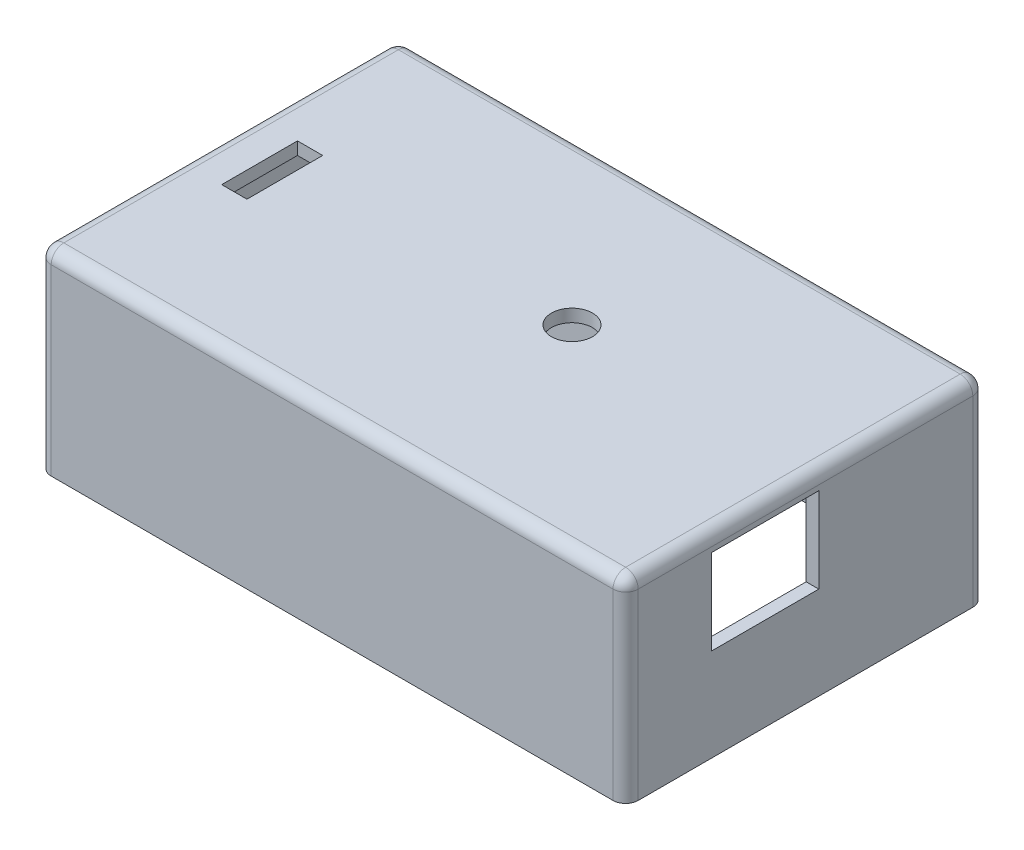
SolidWorks part; units mm, degrees
ref_plane "Front Plane" through (0, 0, 0) normal (0, 0, 1) x (1, 0, 0)
ref_plane "Top Plane" through (0, 0, 0) normal (0, 1, 0) x (1, 0, 0)
ref_plane "Right Plane" through (0, 0, 0) normal (1, 0, 0) x (0, 0, -1)
sketch "Sketch1" plane through (0, 0, 0) normal (0, 1, 0) x (1, 0, 0)
  line L1 (-46.5, -28.5) -> (46.5, -28.5)
  line L2 (-46.5, -28.5) -> (-46.5, 28.5)
  line L3 (-46.5, 28.5) -> (46.5, 28.5)
  line L4 (46.5, -28.5) -> (46.5, 28.5)
  line L5 (-46.5, -28.5) -> (46.5, 28.5) construction
  line L6 (-46.5, 28.5) -> (46.5, -28.5) construction
  point P0 (0, 0)
  dimension "D1" = 93
  dimension "D2" = 57
extrude "Boss-Extrude1" add sketch "Sketch1" along normal blind 31
shell "Shell1" thickness 2
sketch "Sketch2" plane through (46.5, 0, 0) normal (1, 0, 0) x (0, 0, -1)
  line L0 (-28.5, 0) -> (28.5, 0) construction
  line L1 (-14.9, 14.7) -> (2.1, 14.7)
  line L2 (-14.9, 14.7) -> (-14.9, 28.2)
  line L3 (-14.9, 28.2) -> (2.1, 28.2)
  line L4 (2.1, 14.7) -> (2.1, 28.2)
  line L5 (-14.9, 14.7) -> (2.1, 28.2) construction
  line L6 (-14.9, 28.2) -> (2.1, 14.7) construction
  line L7 (-28.5, 31) -> (-28.5, 0) construction
  point P0 (-6.4, 21.45)
  dimension "D1" = 17
  dimension "D2" = 13.5
  dimension "D3" = 14.7
  dimension "D4" = 13.6
extrude "Cut-Extrude1" cut sketch "Sketch2" against normal up to surface (2 mm away) up to face at (44.5, 14.5, 0)
sketch "Sketch3" plane through (0, 31, 0) normal (0, 1, 0) x (1, 0, 0)
  line L0 (-46.5, -28.5) -> (46.5, -28.5) construction
  line L2 (-46.5, 28.5) -> (-46.5, -28.5) construction
  circle A0 centre (7, 2.5) radius 3.25
  dimension "D1" = 6.5
  dimension "D2" = 31
  dimension "D3" = 53.5
extrude "Cut-Extrude2" cut sketch "Sketch3" against normal up to surface (2 mm away) up to face at (0, 29, 0)
sketch "Sketch4" plane through (0, 31, 0) normal (0, 1, 0) x (1, 0, 0)
  line L0 (-46.5, 28.5) -> (-46.5, -28.5) construction
  line L1 (-39.9873, -6) -> (-35.9873, -6)
  line L2 (-39.9873, -6) -> (-39.9873, 6)
  line L3 (-39.9873, 6) -> (-35.9873, 6)
  line L4 (-35.9873, -6) -> (-35.9873, 6)
  line L5 (-39.9873, -6) -> (-35.9873, 6) construction
  line L6 (-39.9873, 6) -> (-35.9873, -6) construction
  point P0 (-37.9873, 0)
  dimension "D1" = 4
  dimension "D2" = 12
  dimension "D3" = 6.5127
extrude "Cut-Extrude3" cut sketch "Sketch4" against normal up to surface (2 mm away) up to face at (7, 29, -5.75)
sketch "Sketch5" plane through (0, 0, -28.5) normal (0, 0, -1) x (-1, 0, 0)
  line L0 (46.5, 15.5) -> (-13.5295, 15.5) construction
  line L1 (46.5, 31) -> (46.5, 0) construction
  circle A0 centre (31.5, 15.5) radius 3
  circle A1 centre (16.5, 15.5) radius 3.25
  dimension "D1" = 6
  dimension "D2" = 6.5
  dimension "D3" = 15
  dimension "D4" = 15
extrude "Cut-Extrude4" cut sketch "Sketch5" against normal up to surface (2 mm away) up to face at (0, 14.5, -26.5)
sketch "Sketch6" plane through (-46.5, 0, 0) normal (-1, 0, 0) x (0, 0, 1)
  line L0 (-28.5, 15.5) -> (16.5493, 15.5) construction
  line L1 (-28.5, 31) -> (-28.5, 0) construction
  circle A0 centre (-18.5, 15.5) radius 5
  dimension "D1" = 10
  dimension "D2" = 10
extrude "Cut-Extrude5" cut sketch "Sketch6" against normal up to surface (2 mm away) up to face at (-44.5, 14.5, 0)
fillet "Fillet1" radius 2 8 edges at (46.5, 15.5, -28.5) (46.5, 15.5, 28.5) (-46.5, 15.5, -28.5) (-46.5, 15.5, 28.5) (46.5, 31, 0) (0, 31, 28.5) (0, 31, -28.5) (-46.5, 31, 0)
sketch "Sketch7" plane through (0, 0, 0) normal (0, -1, 0) x (1, 0, 0)
  line L0 (-45.6, 27.6) -> (-45.6, -27.6)
  line L1 (-44.5, 26.5) -> (44.5, 26.5)
  line L2 (-44.5, 26.5) -> (-44.5, -26.5)
  line L3 (-44.5, -26.5) -> (44.5, -26.5)
  line L4 (44.5, 26.5) -> (44.5, -26.5)
  line L5 (-45.6, -27.6) -> (45.6, -27.6)
  line L6 (45.6, 27.6) -> (45.6, -27.6)
  line L7 (-45.6, 27.6) -> (45.6, 27.6)
  dimension "D1" = 1.1
extrude "Cut-Extrude6" cut sketch "Sketch7" against normal blind 1.1
ref_plane "Plane1" through (0, 1.7, 0) normal (0, -1, 0) x (-1, 0, 0)
sketch "Sketch8" plane through (0, 1.7, 0) normal (0, -1, 0) x (-1, 0, 0)
  line L1 (-44.5, 26.5) -> (-34.5, 26.5)
  line L2 (-44.5, 26.5) -> (-44.5, 16.5)
  line L3 (-44.5, 16.5) -> (-34.5, 16.5)
  line L4 (-34.5, 26.5) -> (-34.5, 16.5)
  line L5 (-44.5, -26.5) -> (-34.5, -26.5)
  line L6 (-44.5, -26.5) -> (-44.5, -16.5)
  line L7 (-44.5, -16.5) -> (-34.5, -16.5)
  line L8 (-34.5, -26.5) -> (-34.5, -16.5)
  line L9 (44.5, -26.5) -> (34.5, -26.5)
  line L10 (44.5, -26.5) -> (44.5, -16.5)
  line L11 (44.5, -16.5) -> (34.5, -16.5)
  line L12 (34.5, -26.5) -> (34.5, -16.5)
  line L13 (44.5, 26.5) -> (34.5, 26.5)
  line L14 (44.5, 26.5) -> (44.5, 16.5)
  line L15 (44.5, 16.5) -> (34.5, 16.5)
  line L16 (34.5, 26.5) -> (34.5, 16.5)
  dimension "D1" = 10
  dimension "D2" = 10
  dimension "D3" = 10
  dimension "D4" = 10
  dimension "D5" = 10
  dimension "D6" = 10
  dimension "D7" = 10
  dimension "D8" = 10
extrude "Boss-Extrude2" add sketch "Sketch8" against normal blind 5
